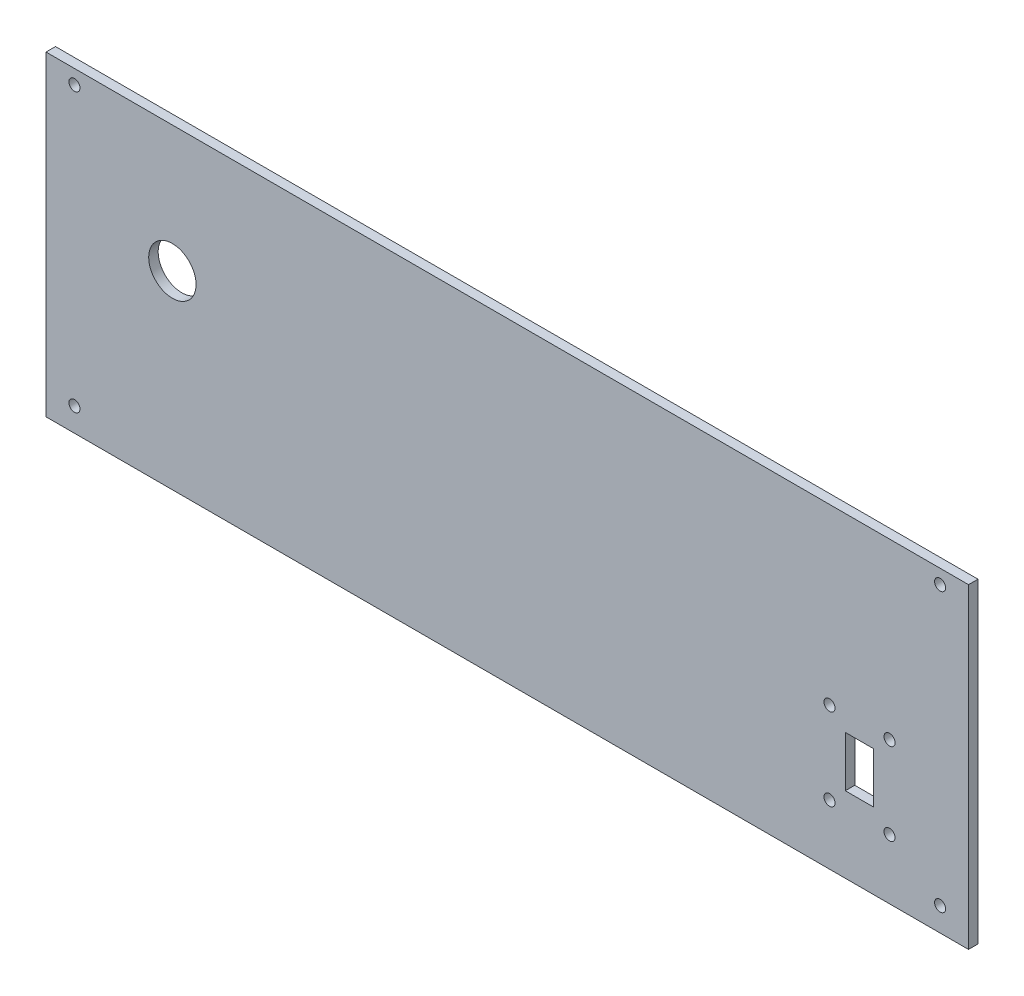
SolidWorks part; units mm, degrees
ref_plane "Front Plane" through (0, 0, 0) normal (0, 0, 1) x (1, 0, 0)
ref_plane "Top Plane" through (0, 0, 0) normal (0, 1, 0) x (1, 0, 0)
ref_plane "Right Plane" through (0, 0, 0) normal (1, 0, 0) x (0, 0, -1)
sketch "Sketch1" plane through (0, 0, 0) normal (0, 0, 1) x (1, 0, 0)
  line L1 (0, 0) -> (300, 0)
  line L2 (0, 0) -> (0, 100)
  line L3 (0, 100) -> (300, 100)
  line L4 (300, 0) -> (300, 100)
  dimension "D1" = 300
  dimension "D2" = 100
extrude "Boss-Extrude1" add sketch "Sketch1" along normal blind 3
sketch "Sketch3" plane through (0, 0, 0) normal (0, 0, -1) x (-1, 0, 0)
  line L0 (0, 0) -> (-300, 0) construction
  line L1 (0, 100) -> (-8, 100)
  line L2 (0, 100) -> (0, 0)
  line L3 (0, 0) -> (-8, 0)
  line L4 (-8, 100) -> (-8, 0)
  dimension "D1" = 8
extrude "Cut-Extrude2" cut sketch "Sketch3" against normal blind 10
sketch "Sketch4" plane through (0, 0, 0) normal (0, 0, -1) x (-1, 0, 0)
  line L0 (-300, 0) -> (-300, 100) construction
  line L1 (-300, 100) -> (-8, 100) construction
  line L2 (-154, 100) -> (-154, 75.8686) construction
  line L3 (-8, 0) -> (-300, 0) construction
  line L4 (-300, 0) -> (-300, 100) construction
  circle A0 centre (-291, 95.5) radius 1.75
  circle A3 centre (-17, 95.5) radius 1.75
  circle A4 centre (-17, 7.5) radius 1.75
  circle A5 centre (-291, 7.5) radius 1.75
  dimension "D4" = 3.5
  dimension "D8" = 9
  dimension "D9" = 3.5
  dimension "D1" = 9
  dimension "D2" = 4.5
  dimension "D5" = 7.5
extrude "Cut-Extrude3" cut sketch "Sketch4" against normal through all
sketch "Sketch5" plane through (0, 0, 0) normal (0, 0, -1) x (-1, 0, 0)
  line L0 (-300, 100) -> (-8, 100) construction
  line L1 (-8, 100) -> (-8, 0) construction
  circle A0 centre (-48, 60) radius 7.5
  dimension "D1" = 15
  dimension "D2" = 40
  dimension "D3" = 40
extrude "Cut-Extrude4" cut sketch "Sketch5" against normal blind 10
sketch "Sketch6" plane through (0, 0, 0) normal (0, 0, -1) x (-1, 0, 0)
  line L0 (-300, 100) -> (-8, 100) construction
  line L1 (-261, 24) -> (-270, 24)
  line L2 (-261, 24) -> (-261, 40)
  line L3 (-261, 40) -> (-270, 40)
  line L4 (-270, 24) -> (-270, 40)
  line L5 (-300, 0) -> (-300, 100) construction
  line L6 (-270, 32) -> (-263.0404, 32) construction
  line L7 (-265.5, 40) -> (-265.5, 26.2232) construction
  circle A0 centre (-275, 45) radius 1.75
  circle A1 centre (-275, 19) radius 1.75
  circle A2 centre (-256, 19) radius 1.75
  circle A3 centre (-256, 45) radius 1.75
  dimension "D5" = 3.5
  dimension "D1" = 16
  dimension "D2" = 9
  dimension "D3" = 60
  dimension "D4" = 30
  dimension "D6" = 5
  dimension "D7" = 5
extrude "Cut-Extrude5" cut sketch "Sketch6" against normal blind 10
